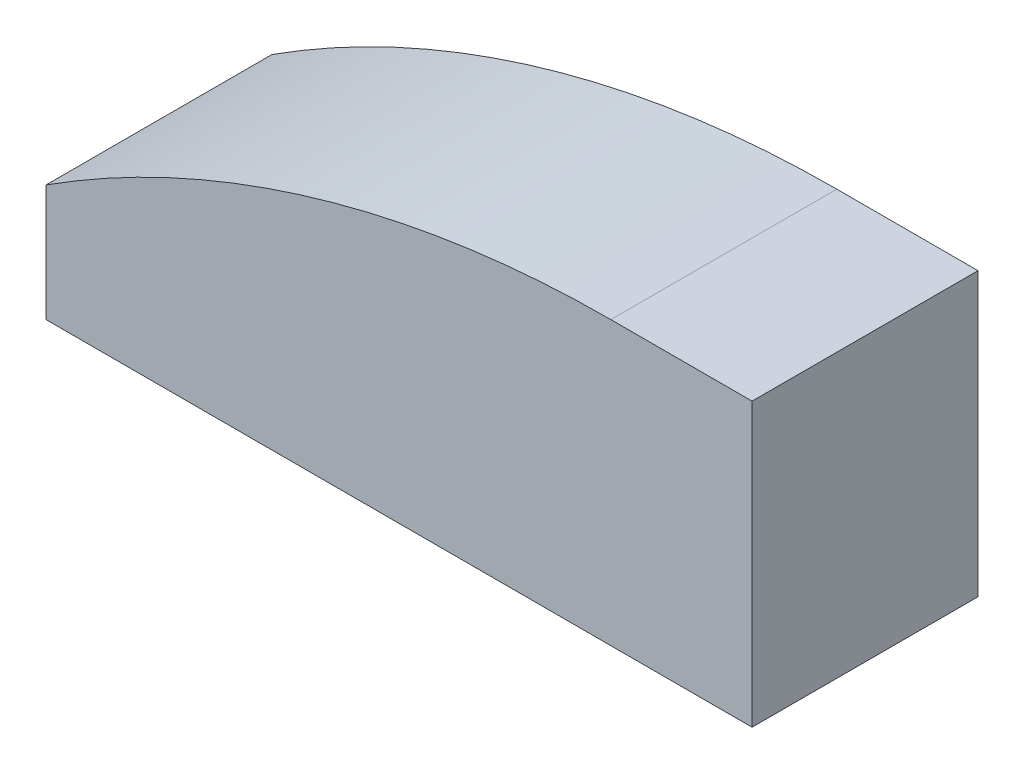
SolidWorks part; units mm, degrees
ref_plane "Front Plane" through (0, 0, 0) normal (0, 0, 1) x (1, 0, 0)
ref_plane "Top Plane" through (0, 0, 0) normal (0, 1, 0) x (1, 0, 0)
ref_plane "Right Plane" through (0, 0, 0) normal (1, 0, 0) x (0, 0, -1)
sketch "Sketch1" plane through (0, 0, 0) normal (0, 0, 1) x (1, 0, 0)
  line L1 (0, -50) -> (-125, -50)
  line L2 (-125, -50) -> (-125, -29.3562)
  line L3 (-25, 0) -> (-125, 0) construction
  line L4 (-25, 0) -> (0, 0)
  line L5 (0, 0) -> (0, -50)
  arc A0 (-125, -29.3562) -> (-25, 0) centre (-25, -185) cw
  dimension "D4" = 185
  dimension "D1" = 25
  dimension "D2" = 125
  dimension "D3" = 50
extrude "Boss-Extrude1" add sketch "Sketch1" along normal mid plane 40
